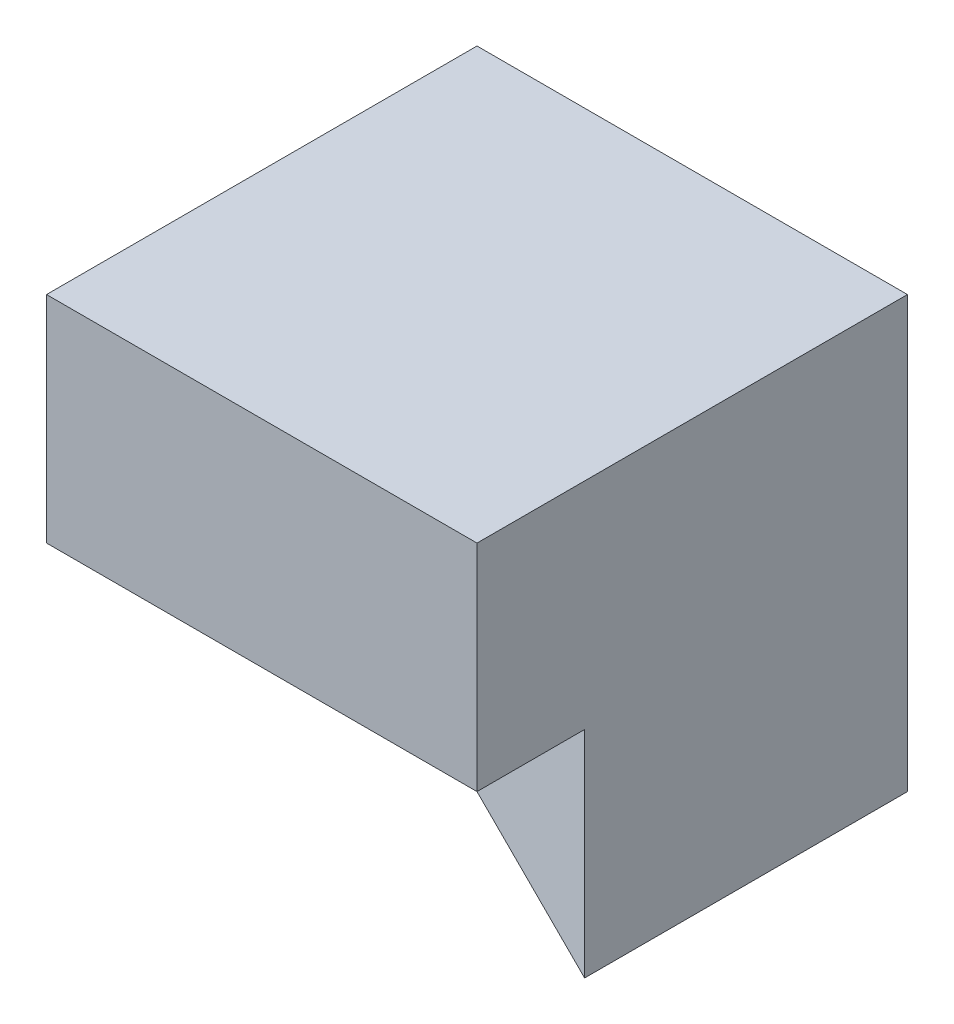
SolidWorks part; units mm, degrees
ref_plane "Front Plane" through (0, 0, 0) normal (0, 0, 1) x (1, 0, 0)
ref_plane "Top Plane" through (0, 0, 0) normal (0, 1, 0) x (1, 0, 0)
ref_plane "Right Plane" through (0, 0, 0) normal (1, 0, 0) x (0, 0, -1)
sketch "Sketch1" plane through (0, 0, 0) normal (0, 0, 1) x (1, 0, 0)
  line L1 (0, 0) -> (40, 0)
  line L2 (0, 0) -> (0, 40)
  line L3 (0, 40) -> (40, 40)
  line L4 (40, 0) -> (40, 40)
  dimension "D1" = 40
  dimension "D2" = 40
extrude "Boss-Extrude1" add sketch "Sketch1" along normal blind 40
sketch "Sketch2" plane through (0, 0, 0) normal (-1, 0, 0) x (0, 0, 1)
  line L1 (40, 0) -> (30, 0)
  line L2 (40, 0) -> (40, 20)
  line L3 (40, 20) -> (30, 20)
  line L4 (30, 0) -> (30, 20)
  dimension "D1" = 10
  dimension "D2" = 20
extrude "Cut-Extrude1" cut sketch "Sketch2" against normal blind 40
sketch "Sketch3" plane through (0, 0, 0) normal (-1, 0, 0) x (0, 0, 1)
  line L1 (30, 0) -> (10, 0)
  line L2 (30, 0) -> (30, 20)
  line L3 (30, 20) -> (10, 20)
  line L4 (10, 0) -> (10, 20)
  dimension "D1" = 20
  dimension "D2" = 20
extrude "Cut-Extrude3" cut sketch "Sketch3" against normal blind 47
ref_plane "Plane1" through (40, 20, 40) normal (0, 0, -1) x (-1, 0, 0)
ref_plane "Plane2" through (0, 20, 0) normal (0, 1, 0) x (1, 0, 0)
sketch "Sketch9" plane through (0, 20, 0) normal (0, 1, 0) x (1, 0, 0)
  line L0 (40, -40) -> (40, -10) construction
  point P0 (40, -30)
  dimension "D1" = 10
ref_plane "Plane3" through (0, 20, 0) normal (0, 1, 0) x (1, 0, 0)
sketch "Sketch10" plane through (0, 20, 0) normal (0, 1, 0) x (1, 0, 0)
  line L0 (40, -30) -> (40, -10)
  line L1 (40, -10) -> (0, -10)
  line L3 (0, -10) -> (40, -30)
extrude "Boss-Extrude5" add sketch "Sketch10" against normal blind 20
